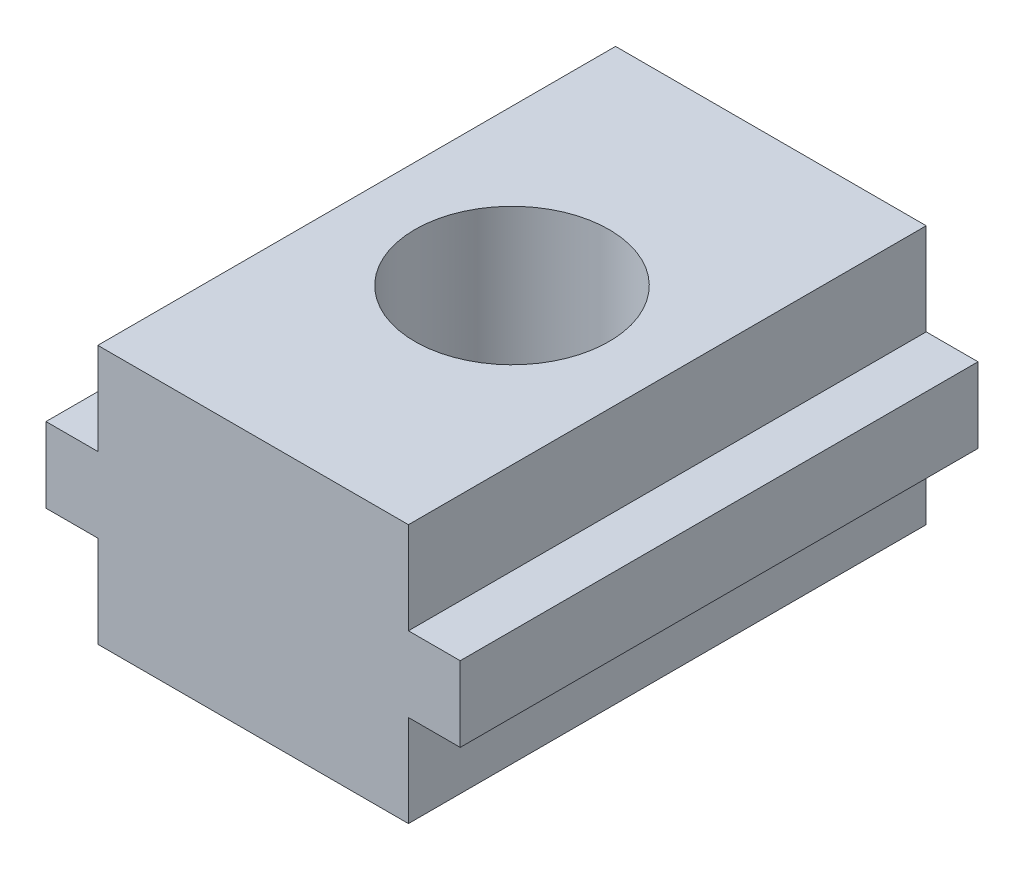
SolidWorks part; units mm, degrees
ref_plane "Front Plane" through (0, 0, 0) normal (0, 0, 1) x (1, 0, 0)
ref_plane "Top Plane" through (0, 0, 0) normal (0, 1, 0) x (1, 0, 0)
ref_plane "Right Plane" through (0, 0, 0) normal (1, 0, 0) x (0, 0, -1)
sketch "Sketch1" plane through (0, 0, 0) normal (0, 0, 1) x (1, 0, 0)
  line L0 (-6, 10) -> (-6, 6.45)
  line L1 (-6, 6.45) -> (-8, 6.45)
  line L2 (-8, 6.45) -> (-8, 3.55)
  line L3 (-8, 3.55) -> (-6, 3.55)
  line L4 (-6, 3.55) -> (-6, 0)
  line L5 (-6, 0) -> (6, 0)
  line L6 (6, 0) -> (6, 3.55)
  line L7 (6, 3.55) -> (8, 3.55)
  line L8 (8, 3.55) -> (8, 6.45)
  line L9 (8, 6.45) -> (6, 6.45)
  line L10 (6, 6.45) -> (6, 10)
  line L11 (6, 10) -> (-6, 10)
  point P8 (7.6718, -12.3849)
  point P13 (15.3839, -7.9357)
  point P14 (13.8019, 4.1267)
  point P15 (0, 0)
  point P18 (0, 0)
  dimension "D1" = 12
  dimension "D2" = 10
  dimension "D3" = 2.9
  dimension "D4" = 2
extrude "Boss-Extrude1" add sketch "Sketch1" along normal mid plane 20
sketch "Sketch2" plane through (0, 10, 0) normal (0, 1, 0) x (1, 0, 0)
  circle A0 centre (0, 0) radius 3.75
  dimension "D1" = 7.5
extrude "Cut-Extrude1" cut sketch "Sketch2" against normal blind 8
sketch "Sketch3" plane through (0, 2, 0) normal (0, 1, 0) x (1, 0, 0)
  circle A0 centre (0, 0) radius 3
  dimension "D1" = 6
extrude "Cut-Extrude2" cut sketch "Sketch3" against normal through all
